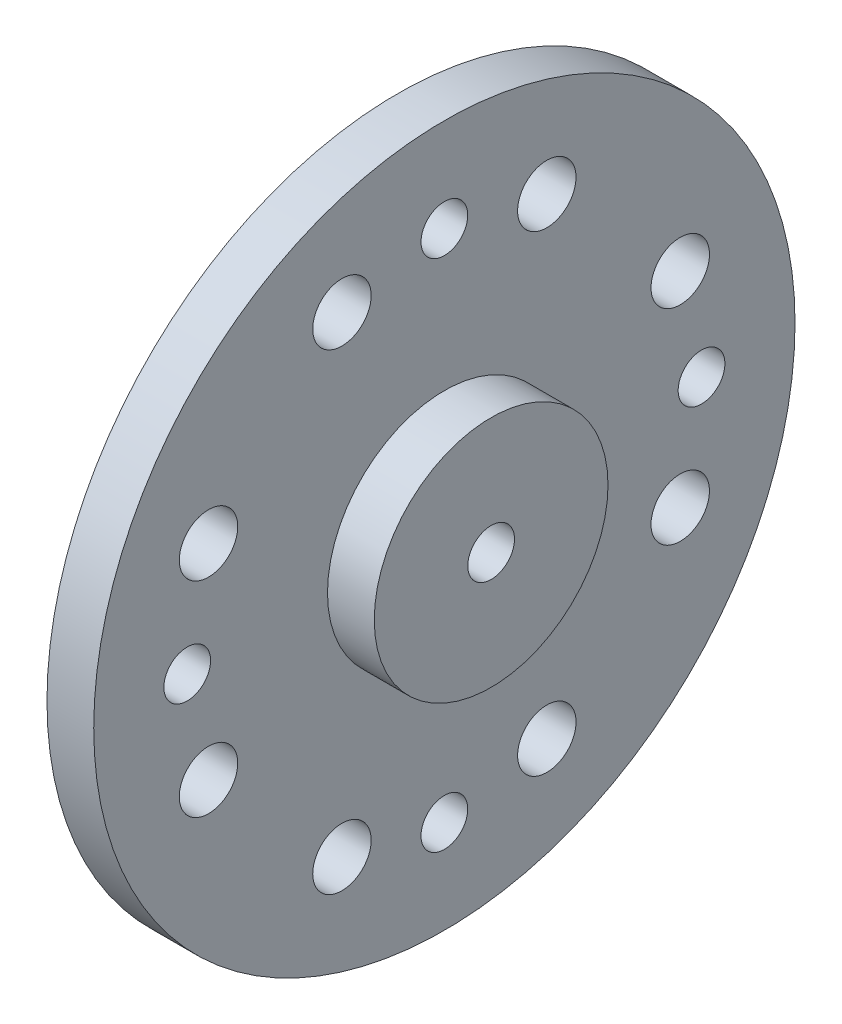
SolidWorks part; units mm, degrees
ref_plane "Front Plane" through (0, 0, 0) normal (0, 0, 1) x (1, 0, 0)
ref_plane "Top Plane" through (0, 0, 0) normal (0, 1, 0) x (1, 0, 0)
ref_plane "Right Plane" through (0, 0, 0) normal (1, 0, 0) x (0, 0, -1)
sketch "Sketch1" plane through (0, 0, 0) normal (0, 0, 1) x (1, 0, 0)
  line L0 (1.8094, 15) -> (1.1906, 15)
  line L1 (0, 0) -> (3, 0)
  line L2 (0, 0) -> (0, 14)
  line L3 (3, 14) -> (3, 15)
  line L4 (3, 0) -> (3, 14)
  line L5 (0, 15) -> (0, 14)
  line L10 (1.1906, 15) -> (0, 15)
  line L14 (3, 15) -> (1.8094, 15)
  dimension "D1" = 3
  dimension "D2" = 15
  dimension "D5" = 1.1906
revolve "Revolve1" add sketch "Sketch1" angle 360 about L1
sketch "Sketch3" plane through (3, 0, 0) normal (1, 0, 0) x (0, 0, -1)
  circle A0 centre (0, 0) radius 1.5
  dimension "D1" = 3
extrude "Extrude1" cut sketch "Sketch3" against normal through all
sketch "Sketch4" plane through (3, 0, 0) normal (1, 0, 0) x (0, 0, -1)
  line L0 (0, -23.8998) -> (0, 29.2964) construction
  line L1 (31.7409, 0) -> (-31.7451, 0) construction
  line L2 (0, 0) -> (18.9307, 32.789) construction
  line L3 (0, 0) -> (-17.3596, 30.0677) construction
  circle A0 centre (0, 11) radius 1
  circle A1 centre (-4.3818, 10.0896) radius 1.25
  circle A2 centre (4.3818, 10.0896) radius 1.25
  circle A3 centre (10.0896, -4.3818) radius 1.25
  circle A4 centre (11, 0) radius 1
  circle A5 centre (10.0896, 4.3818) radius 1.25
  circle A6 centre (-4.3818, -10.0896) radius 1.25
  circle A7 centre (0, -11) radius 1
  circle A8 centre (4.3818, -10.0896) radius 1.25
  circle A9 centre (-10.0896, 4.3818) radius 1.25
  circle A10 centre (-11, 0) radius 1
  circle A11 centre (-10.0896, -4.3818) radius 1.25
  dimension "D1" = 2
  dimension "D5" = 2.5
  dimension "D2" = 11
  dimension "D4" = 30
  dimension "D6" = 11
extrude "Extrude2" cut sketch "Sketch4" against normal through all
sketch "Sketch5" plane through (3, 0, 0) normal (1, 0, 0) x (0, 0, -1)
  circle A0 centre (0, 0) radius 5
  circle A1 centre (0, 0) radius 1
  dimension "D1" = 10
extrude "Boss-Extrude1" add sketch "Sketch5" along normal blind 2
sketch "Sketch6" plane through (0, 0, 0) normal (-1, 0, 0) x (0, 0, 1)
  circle A0 centre (0, 0) radius 15
  circle A1 centre (0, 0) radius 5
  dimension "D1" = 10
extrude "Cut-Extrude2" cut sketch "Sketch6" against normal blind 1
